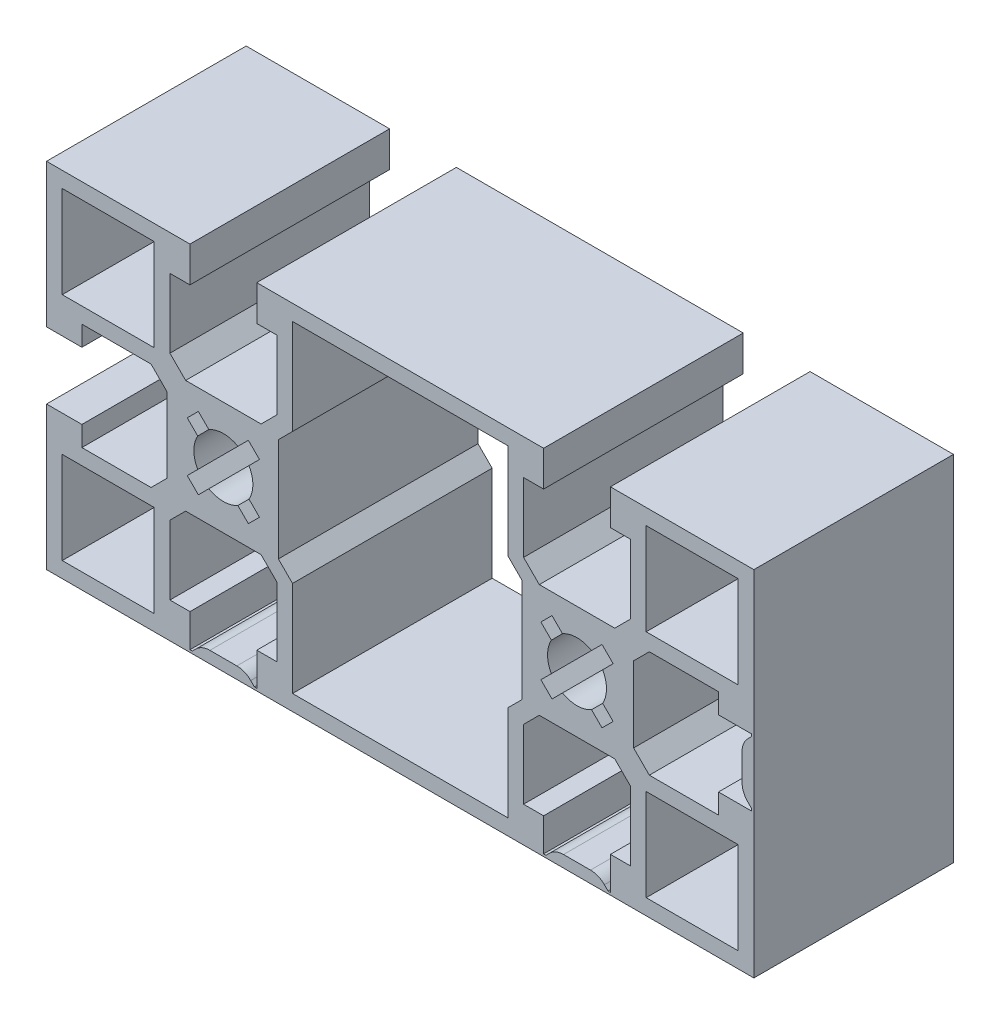
SolidWorks part; units mm, degrees
material "6061 Alloy"
ref_plane "Front Plane" through (0, 0, 0) normal (0, 0, 1) x (1, 0, 0)
ref_plane "Top Plane" through (0, 0, 0) normal (0, 1, 0) x (1, 0, 0)
ref_plane "Right Plane" through (0, 0, 0) normal (1, 0, 0) x (0, 0, -1)
sketch "Sketch1" plane through (0, 0, 0) normal (0, 0, 1) x (1, 0, 0)
  line L0 (19.2372, 1.8485) -> (17.9037, 3.182)
  line L1 (17.9037, -3.182) -> (19.2372, -1.8485)
  line L2 (19.3179, -4.5962) -> (17.9037, -3.182)
  line L3 (20.6514, -3.2627) -> (19.3179, -4.5962)
  line L4 (25.6819, -4.5962) -> (24.3484, -3.2627)
  line L5 (27.0961, -3.182) -> (25.6819, -4.5962)
  line L6 (25.7626, -1.8485) -> (27.0961, -3.182)
  line L7 (27.0961, 3.182) -> (25.7626, 1.8485)
  line L8 (-45.0001, -22.5) -> (44.9999, -22.5)
  line L9 (44.9999, -22.5) -> (44.9999, 22.5)
  line L10 (44.9999, 22.5) -> (26.7499, 22.5)
  line L11 (-45.0001, 22.5) -> (-45.0001, 4.25)
  line L12 (25.6819, 4.5962) -> (27.0961, 3.182)
  line L13 (24.3484, 3.2627) -> (25.6819, 4.5962)
  line L14 (19.3179, 4.5962) -> (20.6514, 3.2627)
  line L15 (17.9037, 3.182) -> (19.3179, 4.5962)
  line L16 (-25.6821, -4.5962) -> (-27.0963, -3.182)
  line L17 (-19.2374, -1.8485) -> (-17.9039, -3.182)
  line L18 (-25.6821, 4.5962) -> (-24.3486, 3.2627)
  line L19 (-27.0963, 3.182) -> (-25.6821, 4.5962)
  line L20 (-27.0963, -3.182) -> (-25.7628, -1.8485)
  line L21 (-17.9039, -3.182) -> (-19.3181, -4.5962)
  line L22 (-20.6516, 3.2627) -> (-19.3181, 4.5962)
  line L23 (-25.7628, 1.8485) -> (-27.0963, 3.182)
  line L24 (42.9999, 20.5) -> (42.9999, 8.8)
  line L25 (31.2999, 20.5) -> (42.9999, 20.5)
  line L26 (31.2999, 8.8) -> (31.2999, 20.5)
  line L27 (42.9999, 8.8) -> (31.2999, 8.8)
  line L28 (42.9999, -20.5) -> (31.2999, -20.5)
  line L29 (42.9999, -8.8) -> (42.9999, -20.5)
  line L30 (31.2999, -8.8) -> (42.9999, -8.8)
  line L31 (31.2999, -20.5) -> (31.2999, -8.8)
  line L32 (-31.3001, -8.8) -> (-31.3001, -20.5)
  line L33 (-31.3001, -20.5) -> (-43.0001, -20.5)
  line L34 (-43.0001, -20.5) -> (-43.0001, -8.8)
  line L35 (-43.0001, -8.8) -> (-31.3001, -8.8)
  line L36 (-31.3001, 8.8) -> (-43.0001, 8.8)
  line L37 (-31.3001, 20.5) -> (-31.3001, 8.8)
  line L38 (-43.0001, 20.5) -> (-31.3001, 20.5)
  line L39 (-43.0001, 8.8) -> (-43.0001, 20.5)
  line L40 (-19.3181, -4.5962) -> (-20.6516, -3.2627)
  line L41 (-19.3181, 4.5962) -> (-17.9039, 3.182)
  line L42 (-24.3486, -3.2627) -> (-25.6821, -4.5962)
  line L43 (-17.9039, 3.182) -> (-19.2374, 1.8485)
  line L44 (-45.0001, -4.25) -> (-45.0001, -22.5)
  line L45 (-26.7501, 22.5) -> (-45.0001, 22.5)
  line L46 (18.2499, 22.5) -> (-18.2501, 22.5)
  line L56 (-40.5001, -4.25) -> (-45.0001, -4.25)
  line L57 (-40.5001, -6.8) -> (-40.5001, -4.25)
  line L58 (-31.7001, -6.8) -> (-40.5001, -6.8)
  line L59 (-29.7001, -4.8) -> (-31.7001, -6.8)
  line L60 (-29.7001, 4.8) -> (-29.7001, -4.8)
  line L61 (-31.7001, 6.8) -> (-29.7001, 4.8)
  line L62 (-40.5001, 6.8) -> (-31.7001, 6.8)
  line L63 (-40.5001, 4.25) -> (-40.5001, 6.8)
  line L64 (-45.0001, 4.25) -> (-40.5001, 4.25)
  line L82 (-26.7501, -22.2) -> (-26.7501, -18)
  line L83 (-26.4501, -22.2) -> (-26.7501, -22.2)
  line L84 (-25.9824, -21.7323) -> (-26.4501, -22.2)
  line L85 (-20.7857, -21) -> (-24.2146, -21)
  line L86 (-18.5501, -22.2) -> (-19.0179, -21.7322)
  line L87 (-18.2501, -22.2) -> (-18.5501, -22.2)
  line L88 (-18.2501, -18) -> (-18.2501, -22.2)
  line L89 (-15.7001, -18) -> (-18.2501, -18)
  line L90 (-15.7001, -9.2) -> (-15.7001, -18)
  line L91 (-17.7001, -7.2) -> (-15.7001, -9.2)
  line L92 (-27.3001, -7.2) -> (-17.7001, -7.2)
  line L93 (-29.3001, -9.2) -> (-27.3001, -7.2)
  line L94 (-29.3001, -18) -> (-29.3001, -9.2)
  line L95 (-26.7501, -18) -> (-29.3001, -18)
  line L110 (18.2499, -22.2) -> (18.2499, -18)
  line L111 (18.5499, -22.2) -> (18.2499, -22.2)
  line L112 (19.0176, -21.7323) -> (18.5499, -22.2)
  line L113 (24.2143, -21) -> (20.7854, -21)
  line L114 (26.4499, -22.2) -> (25.9821, -21.7322)
  line L115 (26.7499, -22.2) -> (26.4499, -22.2)
  line L116 (26.7499, -18) -> (26.7499, -22.2)
  line L117 (29.2999, -18) -> (26.7499, -18)
  line L118 (29.2999, -9.2) -> (29.2999, -18)
  line L119 (27.2999, -7.2) -> (29.2999, -9.2)
  line L120 (17.6999, -7.2) -> (27.2999, -7.2)
  line L121 (15.6999, -9.2) -> (17.6999, -7.2)
  line L122 (15.6999, -18) -> (15.6999, -9.2)
  line L123 (18.2499, -18) -> (15.6999, -18)
  line L138 (15.6999, 18) -> (18.2499, 18)
  line L139 (15.6999, 9.2) -> (15.6999, 18)
  line L140 (17.6999, 7.2) -> (15.6999, 9.2)
  line L141 (27.2999, 7.2) -> (17.6999, 7.2)
  line L142 (29.2999, 9.2) -> (27.2999, 7.2)
  line L143 (29.2999, 18) -> (29.2999, 9.2)
  line L144 (26.7499, 18) -> (29.2999, 18)
  line L145 (26.7499, 22.5) -> (26.7499, 18)
  line L151 (18.2499, 18) -> (18.2499, 22.5)
  line L166 (31.6999, -6.8) -> (29.6999, -4.8)
  line L167 (40.4999, -6.8) -> (31.6999, -6.8)
  line L168 (40.4999, -4.25) -> (40.4999, -6.8)
  line L169 (44.6999, -4.25) -> (40.4999, -4.25)
  line L170 (44.6999, -3.95) -> (44.6999, -4.25)
  line L171 (44.2322, -3.4823) -> (44.6999, -3.95)
  line L172 (43.4999, 1.7144) -> (43.4999, -1.7145)
  line L173 (44.6999, 3.95) -> (44.2321, 3.4822)
  line L174 (44.6999, 4.25) -> (44.6999, 3.95)
  line L175 (40.4999, 4.25) -> (44.6999, 4.25)
  line L176 (40.4999, 6.8) -> (40.4999, 4.25)
  line L177 (31.6999, 6.8) -> (40.4999, 6.8)
  line L178 (29.6999, 4.8) -> (31.6999, 6.8)
  line L179 (29.6999, -4.8) -> (29.6999, 4.8)
  line L194 (-29.3001, 18) -> (-26.7501, 18)
  line L195 (-29.3001, 9.2) -> (-29.3001, 18)
  line L196 (-27.3001, 7.2) -> (-29.3001, 9.2)
  line L197 (-17.7001, 7.2) -> (-27.3001, 7.2)
  line L198 (-15.7001, 9.2) -> (-17.7001, 7.2)
  line L199 (-15.7001, 18) -> (-15.7001, 9.2)
  line L200 (-18.2501, 18) -> (-15.7001, 18)
  line L201 (-18.2501, 22.5) -> (-18.2501, 18)
  line L207 (-26.7501, 18) -> (-26.7501, 22.5)
  line L220 (13.6999, 20.5) -> (13.6999, 8.3716)
  line L221 (13.6999, 8.3716) -> (15.4999, 6.5716)
  line L222 (15.4999, 6.5716) -> (15.4999, -6.5716)
  line L223 (15.4999, -6.5716) -> (13.6999, -8.3716)
  line L224 (13.6999, -8.3716) -> (13.6999, -20.5)
  line L225 (13.6999, -20.5) -> (-13.7001, -20.5)
  line L226 (-13.7001, -20.5) -> (-13.7001, -8.3716)
  line L227 (-13.7001, -8.3716) -> (-15.5001, -6.5716)
  line L228 (-15.5001, -6.5716) -> (-15.5001, 6.5716)
  line L229 (-15.5001, 6.5716) -> (-13.7001, 8.3716)
  line L230 (-13.7001, 8.3716) -> (-13.7001, 20.5)
  line L231 (-13.7001, 20.5) -> (13.6999, 20.5)
  arc A0 (19.2372, 1.8485) -> (19.2372, -1.8485) centre (22.4999, 0) ccw
  arc A1 (20.6514, -3.2627) -> (24.3484, -3.2627) centre (22.4999, 0) ccw
  arc A4 (25.7626, -1.8485) -> (25.7626, 1.8485) centre (22.4999, 0) ccw
  arc A5 (24.3484, 3.2627) -> (20.6514, 3.2627) centre (22.4999, 0) ccw
  arc A8 (-24.3486, -3.2627) -> (-20.6516, -3.2627) centre (-22.5001, 0) ccw
  arc A9 (-25.7628, 1.8485) -> (-25.7628, -1.8485) centre (-22.5001, 0) ccw
  arc A10 (-24.2146, -21) -> (-25.9824, -21.7323) centre (-24.2146, -23.5) ccw
  arc A11 (-19.0179, -21.7322) -> (-20.7857, -21) centre (-20.7857, -23.5) ccw
  arc A12 (-20.6516, 3.2627) -> (-24.3486, 3.2627) centre (-22.5001, 0) ccw
  arc A13 (-19.2374, -1.8485) -> (-19.2374, 1.8485) centre (-22.5001, 0) ccw
  arc A14 (20.7854, -21) -> (19.0176, -21.7323) centre (20.7854, -23.5) ccw
  arc A15 (25.9821, -21.7322) -> (24.2143, -21) centre (24.2143, -23.5) ccw
  arc A22 (43.4999, -1.7145) -> (44.2322, -3.4823) centre (45.9999, -1.7145) ccw
  arc A23 (44.2321, 3.4822) -> (43.4999, 1.7144) centre (45.9999, 1.7144) ccw
extrude "Boss-Extrude1" add sketch "Sketch1" along normal blind 25.4 contours L62 L61 L60 L59 L58 L57 L56 L44 L8 L9 L10 L145 L144 L143 L142 L141 L140 L139 L138 L151 L46 L201 L200 L199 L198 L197 L196 L195 L194 L207 L45 L11 L64 L63 | A8 L40 L21 L17 A13 L43 L41 L22 A12 L18 L19 L23 A9 L20 L16 L42 | A1 L4 L5 L6 A4 L7 L12 L13 A5 L14 L15 L0 A0 L1 L2 L3 | L120 L119 L118 L117 L116 L115 L114 A15 L113 A14 L112 L111 L110 L123 L122 L121 | L179 L178 L177 L176 L175 L174 L173 A23 L172 A22 L171 L170 L169 L168 L167 L166 | L92 L91 L90 L89 L88 L87 L86 A11 L85 A10 L84 L83 L82 L95 L94 L93 | L35 L32 L33 L34 | L36 L39 L38 L37 | L220 L221 L222 L223 L224 L225 L226 L227 L228 L229 L230 L231 | L26 L25 L24 L27 | L31 L30 L29 L28
